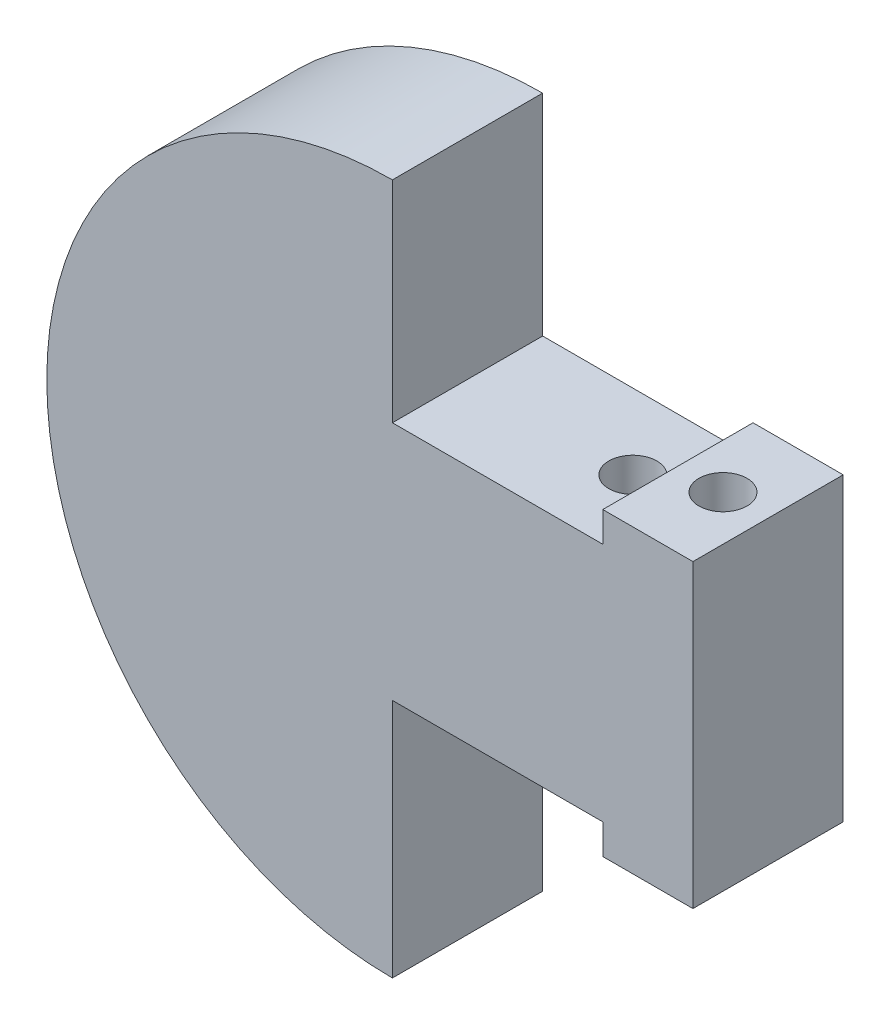
SolidWorks part; units mm, degrees
ref_plane "Front" through (0, 0, 0) normal (0, 0, 1) x (1, 0, 0)
ref_plane "Top" through (0, 0, 0) normal (0, 1, 0) x (1, 0, 0)
ref_plane "Right" through (0, 0, 0) normal (1, 0, 0) x (0, 0, -1)
sketch "Sketch1" plane through (0, 0, 0) normal (0, 0, 1) x (1, 0, 0)
  line L0 (-11, 0) -> (-1, 0) construction
  line L1 (-1, 0) -> (9, 0) construction
  line L2 (0, -11) -> (0, -3)
  line L3 (0, 5) -> (7, 5)
  line L4 (10, 6) -> (7, 6)
  line L5 (7, 6) -> (7, 5)
  line L6 (0, -3) -> (7, -3)
  line L7 (10, 6) -> (10, -4)
  line L8 (7, -3) -> (7, -4)
  line L9 (0, 12) -> (0, 5)
  line L11 (7, -4) -> (10, -4)
  arc A1 (0, 12) -> (0, -11) centre (0, 0.5) ccw
extrude "Boss-Extrude1" add sketch "Sketch1" along normal blind 5
sketch "Sketch2" plane through (0, 0, 0) normal (0, 1, 0) x (1, 0, 0)
  line L0 (10, -2.5) -> (8.5, -2.5) construction
  line L2 (8.5, -2.5) -> (5.5, -2.5) construction
  circle A0 centre (8.5, -2.5) radius 0.8
  circle A1 centre (5.5, -2.5) radius 0.8
extrude "Cut-Extrude1" cut sketch "Sketch2" against normal through all from offset 11
